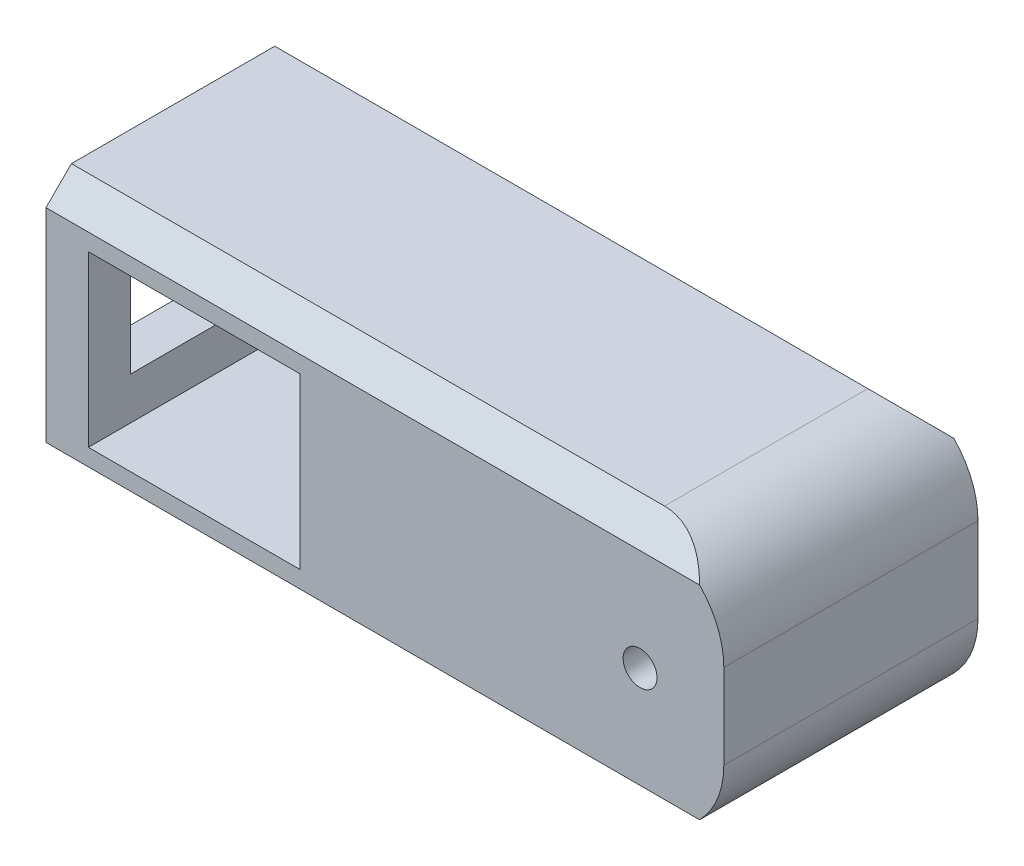
SolidWorks part; units mm, degrees
ref_plane "Front Plane" through (0, 0, 0) normal (0, 0, 1) x (1, 0, 0)
ref_plane "Top Plane" through (0, 0, 0) normal (0, 1, 0) x (1, 0, 0)
ref_plane "Right Plane" through (0, 0, 0) normal (1, 0, 0) x (0, 0, -1)
sketch "Sketch1" plane through (0, 0, 0) normal (0, 1, 0) x (1, 0, 0)
  line L1 (-40, 15) -> (40, 15)
  line L2 (-40, 15) -> (-40, -15)
  line L3 (-40, -15) -> (40, -15)
  line L4 (40, 15) -> (40, -15)
  line L5 (-40, 15) -> (40, -15) construction
  line L6 (-40, -15) -> (40, 15) construction
  point P0 (0, 0)
  dimension "D1" = 80
  dimension "D2" = 30
extrude "Boss-Extrude1" add sketch "Sketch1" along normal blind 30
sketch "Sketch2" plane through (0, 0, 15) normal (0, 0, 1) x (1, 0, 0)
  circle A0 centre (30.1149, 15) radius 2
  dimension "D1" = 4
extrude "Cut-Extrude1" cut sketch "Sketch2" against normal blind 30
chamfer "Chamfer1" distance 3 angle 45 4 edges at (0, 0, 15) (0, 0, -15) (0, 30, -15) (0, 30, 15)
sketch "Sketch3" plane through (0, 0, -15) normal (0, 0, -1) x (-1, 0, 0)
  line L0 (-40, 30) -> (40, 30) construction
  line L1 (35, 5) -> (10, 5)
  line L2 (35, 5) -> (35, 25)
  line L3 (35, 25) -> (10, 25)
  line L4 (10, 5) -> (10, 25)
  line L5 (40, 27) -> (40, 3) construction
  dimension "D1" = 20
  dimension "D2" = 5
  dimension "D3" = 5
  dimension "D4" = 25
extrude "Cut-Extrude2" cut sketch "Sketch3" against normal blind 30
sketch "Sketch4" plane through (-40, 0, 0) normal (-1, 0, 0) x (0, 0, 1)
  line L0 (-15, 27) -> (-15, 3) construction
  line L1 (-10, 20) -> (10, 20)
  line L2 (-10, 20) -> (-10, 10)
  line L3 (-10, 10) -> (10, 10)
  line L4 (10, 20) -> (10, 10)
  line L5 (-10, 20) -> (10, 10) construction
  line L6 (-10, 10) -> (10, 20) construction
  line L7 (-12, 30) -> (12, 30) construction
  point P0 (0, 15)
  dimension "D1" = 20
  dimension "D2" = 10
  dimension "D3" = 5
  dimension "D4" = 10
extrude "Cut-Extrude3" cut sketch "Sketch4" against normal blind 20
fillet "Fillet1" radius 10 2 edges at (40, 0, 0) (40, 30, 0)
